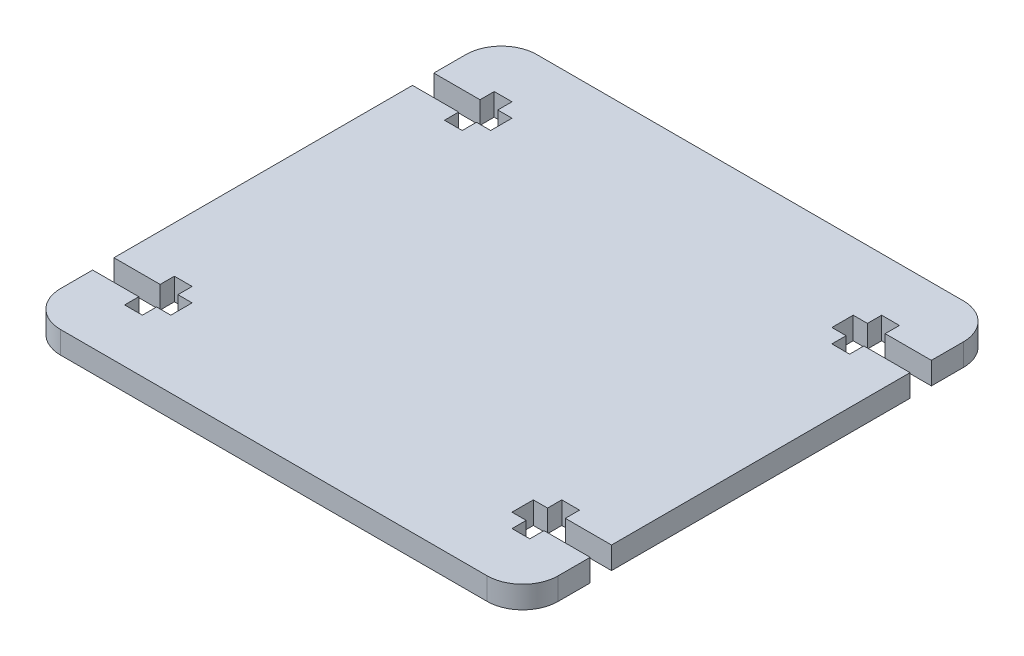
SolidWorks part; units mm, degrees
ref_plane "Front Plane" through (0, 0, 0) normal (0, 0, 1) x (1, 0, 0)
ref_plane "Top Plane" through (0, 0, 0) normal (0, 1, 0) x (1, 0, 0)
ref_plane "Right Plane" through (0, 0, 0) normal (1, 0, 0) x (0, 0, -1)
sketch "Sketch1" plane through (0, 0, 0) normal (0, 1, 0) x (1, 0, 0)
  line L0 (0, 22.5) -> (35, 22.5) construction
  line L1 (0, 33.5) -> (35, 33.5)
  line L2 (0, 33.5) -> (0, 0)
  line L3 (0, 0) -> (35, 0)
  line L4 (35, 33.5) -> (35, 24)
  line L5 (35, 24) -> (28.5, 24)
  line L6 (28.5, 24) -> (28.5, 26)
  line L7 (28.5, 26) -> (26, 26)
  line L8 (26, 26) -> (26, 24)
  line L9 (26, 24) -> (24, 24)
  line L10 (24, 24) -> (24, 21)
  line L11 (24, 21) -> (26, 21)
  line L12 (26, 21) -> (26, 19)
  line L13 (26, 19) -> (28.5, 19)
  line L14 (28.5, 19) -> (28.5, 21)
  line L15 (28.5, 21) -> (35, 21)
  line L16 (35, 21) -> (35, 0)
  point P17 (24, 22.5)
  dimension "D1" = 35
  dimension "D2" = 2.5
  dimension "D3" = 9
  dimension "D4" = 2
  dimension "D5" = 3
  dimension "D6" = 7.5
  dimension "D7" = 7
  dimension "D8" = 22.5
extrude "Boss-Extrude1" add sketch "Sketch1" along normal mid plane 3.125
mirror "Mirror1" about plane through (0, 0, 0) normal (1, 0, 0) of "Boss-Extrude1"
mirror "Mirror4" about plane through (0, 0, 0) normal (0, 0, 1) of "Mirror1", "Boss-Extrude1"
fillet "Fillet1" radius 5 4 edges at (-35, 0, 33.5) (35, 0, 33.5) (35, 0, -33.5) (-35, 0, -33.5)
